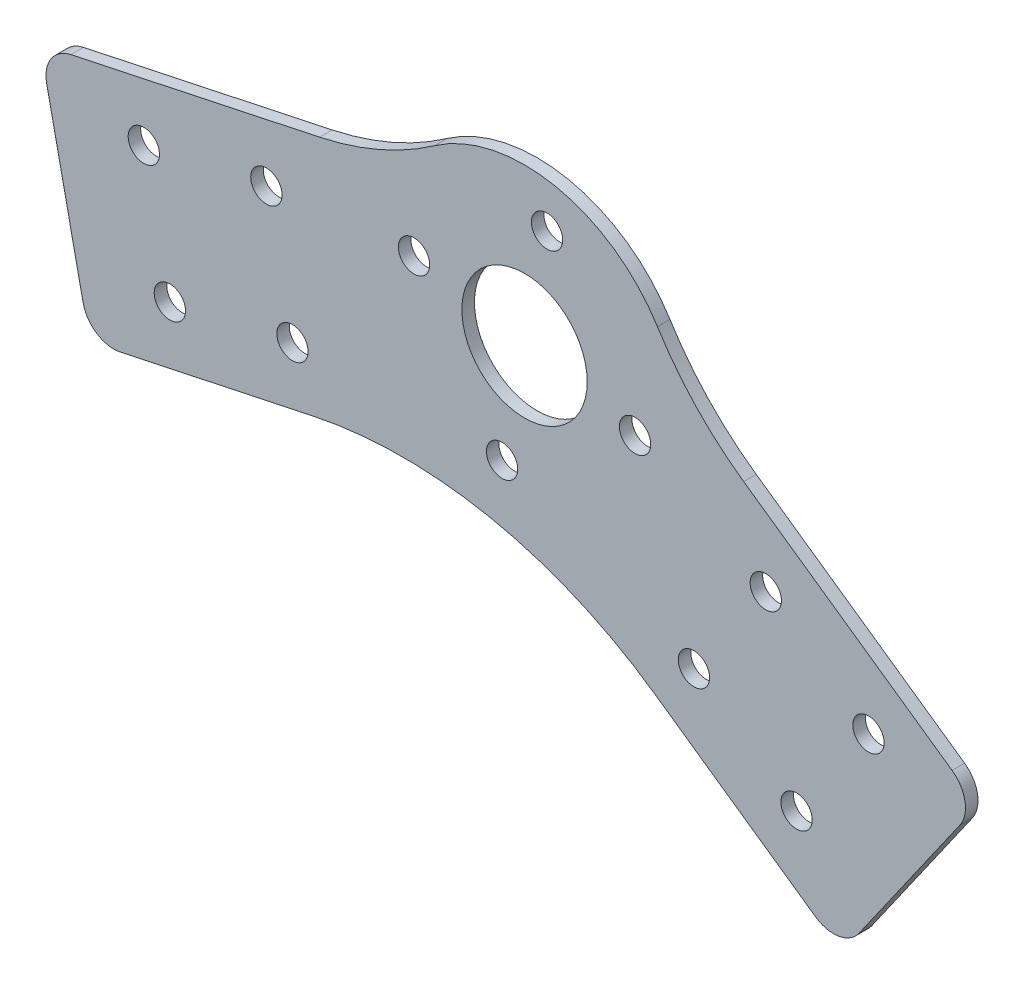
SolidWorks part; units mm, degrees
ref_plane "Front Plane" through (0, 0, 0) normal (0, 0, 1) x (1, 0, 0)
ref_plane "Top Plane" through (0, 0, 0) normal (0, 1, 0) x (1, 0, 0)
ref_plane "Right Plane" through (0, 0, 0) normal (1, 0, 0) x (0, 0, -1)
sketch "Sketch1" plane through (0, 0, 0) normal (0, 0, 1) x (1, 0, 0)
  line L0 (0, 0) -> (-125.5766, -26.6921) construction
  line L1 (102.9503, -72.0866) -> (0, 0) construction
  line L2 (0, 0) -> (0, -101.1714) construction
  line L3 (-48.9074, -10.3956) -> (-52.24, 5.2833) construction
  line L4 (40.9576, -28.6788) -> (56.3568, -6.6865) construction
  line L5 (-77.3114, 2.9914) -> (-69.4107, -34.1782)
  line L6 (-69.4107, -34.1782) -> (-4.1306, -20.3025)
  line L7 (0, 0) -> (4.9842, 24.4981) construction
  line L8 (-4.1306, -20.3025) -> (50.5385, -58.5821)
  line L9 (50.5385, -58.5821) -> (72.3344, -27.4543)
  line L10 (72.3344, -27.4543) -> (24.2076, 6.2444)
  line L12 (-77.3114, 2.9914) -> (-19.8433, 15.2066)
  circle A0 centre (-60.768, -2.6932) radius 2.5
  circle A1 centre (-56.6097, -22.2562) radius 2.5
  circle A2 centre (-37.0468, -18.0979) radius 2.5
  circle A3 centre (-41.205, 1.465) radius 2.5
  circle A4 centre (38.5018, -14.7515) radius 2.5
  circle A5 centre (27.0303, -31.1346) radius 2.5
  circle A6 centre (43.4134, -42.6061) radius 2.5
  circle A7 centre (54.8849, -26.2231) radius 2.5
  circle A8 centre (0, 0) radius 10
  arc A9 (24.2076, 6.2444) -> (-19.8433, 15.2066) centre (0, 0) ccw
  circle A10 centre (3.5886, 17.6386) radius 2.5
  circle A11 centre (17.6386, -3.5886) radius 2.5
  circle A12 centre (-3.5886, -17.6386) radius 2.5
  circle A13 centre (-17.6386, 3.5886) radius 2.5
  point P30 (61.4364, -43.0182)
  point P47 (0, 0)
  dimension "D3" = 5
  dimension "D6" = 5
  dimension "D7" = 10
  dimension "D9" = 20
  dimension "D17" = 50
  dimension "D18" = 5
  dimension "D1" = 55
  dimension "D2" = 78
  dimension "D4" = 10
  dimension "D5" = 10
  dimension "D8" = 10
  dimension "D10" = 50
  dimension "D11" = 50
  dimension "D12" = 19
  dimension "D13" = 19
  dimension "D14" = 15
  dimension "D15" = 38
  dimension "D16" = 15
  dimension "D19" = 18
  dimension "D20" = 4
extrude "Boss-Extrude1" add sketch "Sketch1" along normal blind 2
fillet "Fillet1" radius 50 2 edges at (-19.8433, 15.2066, 1) (24.2076, 6.2444, 1)
fillet "Fillet2" radius 70 1 edges at (-4.1306, -20.3025, 1)
fillet "Fillet3" radius 5 4 edges at (72.3344, -27.4543, 1) (50.5385, -58.5821, 1) (-69.4107, -34.1782, 1) (-77.3114, 2.9914, 1)
